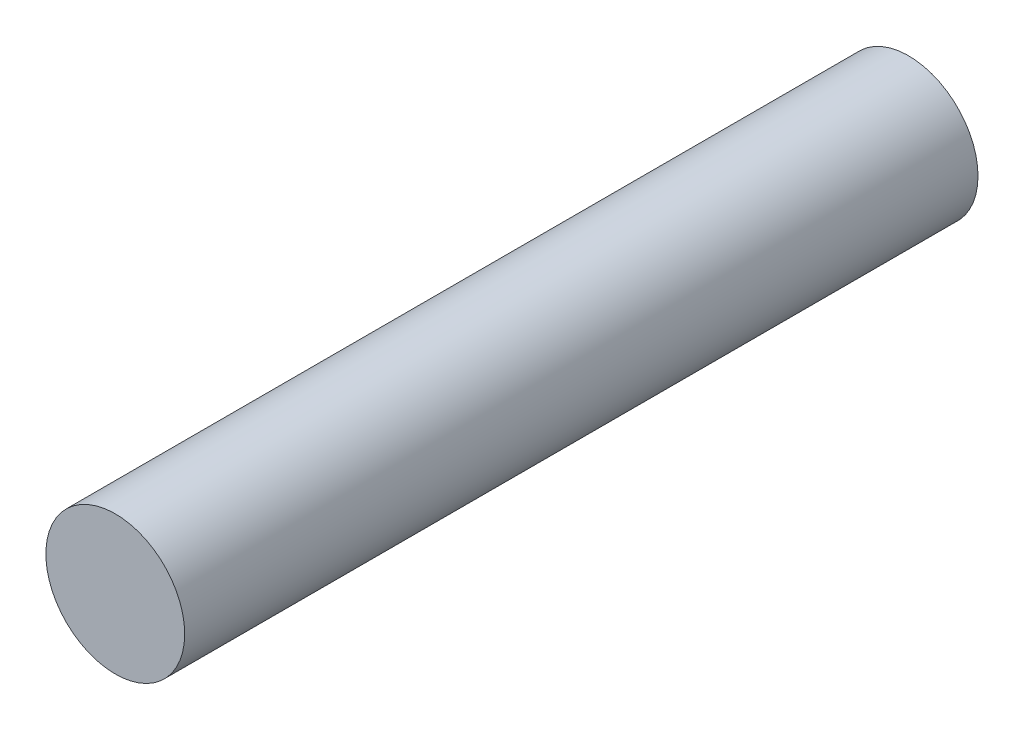
SolidWorks part; units mm, degrees
ref_plane "前视基准面" through (0, 0, 0) normal (0, 0, 1) x (1, 0, 0)
ref_plane "上视基准面" through (0, 0, 0) normal (0, 1, 0) x (1, 0, 0)
ref_plane "右视基准面" through (0, 0, 0) normal (1, 0, 0) x (0, 0, -1)
sketch "草图1" plane through (0, 0, 0) normal (0, 0, 1) x (1, 0, 0)
  circle A0 centre (0, 0) radius 70
  dimension "D1" = 140
extrude "凸台-拉伸1" add sketch "草图1" along normal blind 800
